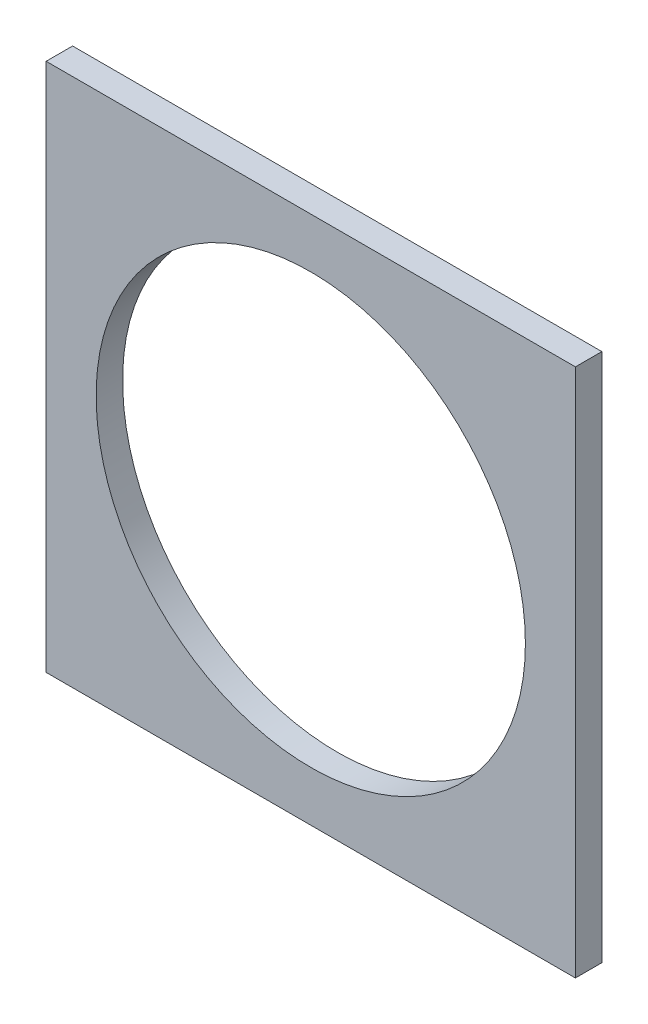
SolidWorks part; units mm, degrees
ref_plane "Front Plane" through (0, 0, 0) normal (0, 0, 1) x (1, 0, 0)
ref_plane "Top Plane" through (0, 0, 0) normal (0, 1, 0) x (1, 0, 0)
ref_plane "Right Plane" through (0, 0, 0) normal (1, 0, 0) x (0, 0, -1)
sketch "Sketch1" plane through (0, 0, 0) normal (0, 0, 1) x (1, 0, 0)
  line L1 (-63.5, 63.5) -> (63.5, 63.5)
  line L2 (-63.5, 63.5) -> (-63.5, -63.5)
  line L3 (-63.5, -63.5) -> (63.5, -63.5)
  line L4 (63.5, 63.5) -> (63.5, -63.5)
  line L5 (-63.5, 63.5) -> (63.5, -63.5) construction
  line L6 (-63.5, -63.5) -> (63.5, 63.5) construction
  point P0 (0, 0)
  dimension "D1" = 127
  dimension "D2" = 127
extrude "Boss-Extrude1" add sketch "Sketch1" along normal blind 6.35
sketch "Sketch2" plane through (0, 0, 6.35) normal (0, 0, 1) x (1, 0, 0)
  circle A0 centre (0, 0) radius 51.5
  dimension "D1" = 103
extrude "Cut-Extrude1" cut sketch "Sketch2" against normal up to next
